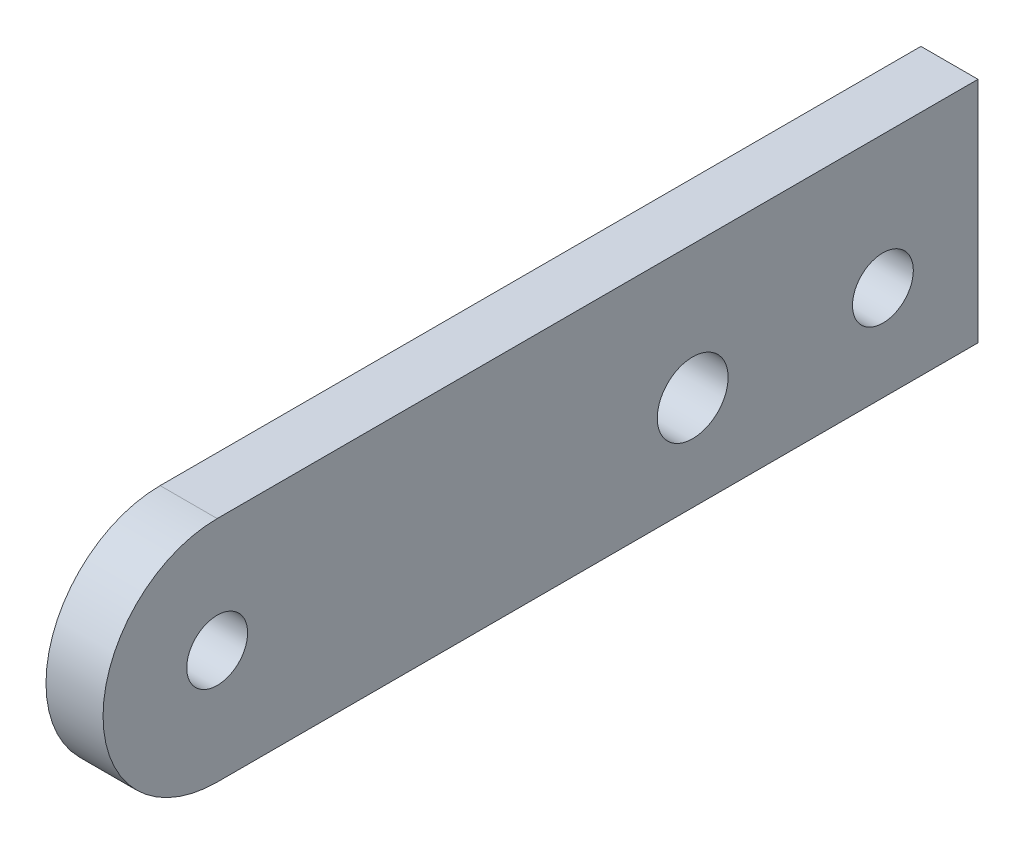
SolidWorks part; units mm, degrees
ref_plane "Front Plane" through (0, 0, 0) normal (0, 0, 1) x (1, 0, 0)
ref_plane "Top Plane" through (0, 0, 0) normal (0, 1, 0) x (1, 0, 0)
ref_plane "Right Plane" through (0, 0, 0) normal (1, 0, 0) x (0, 0, -1)
sketch "Sketch1" plane through (0, 0, 0) normal (1, 0, 0) x (0, 0, -1)
  line L0 (0, 6) -> (40, 6)
  line L1 (40, 6) -> (40, -6)
  line L2 (40, -6) -> (0, -6)
  line L3 (40, -1) -> (10.1577, -1) construction
  circle A0 centre (0, 0) radius 6
  circle A1 centre (0, 0) radius 1.6
  circle A2 centre (35, -1) radius 1.6
  circle A3 centre (25, -1) radius 1.8628
  dimension "D1" = 12
  dimension "D2" = 3.2
  dimension "D4" = 3.2
  dimension "D6" = 5
  dimension "D7" = 3.7256
  dimension "D8" = 10
  dimension "D3" = 40
  dimension "D5" = 7
extrude "Boss-Extrude1" add sketch "Sketch1" along normal blind 3
